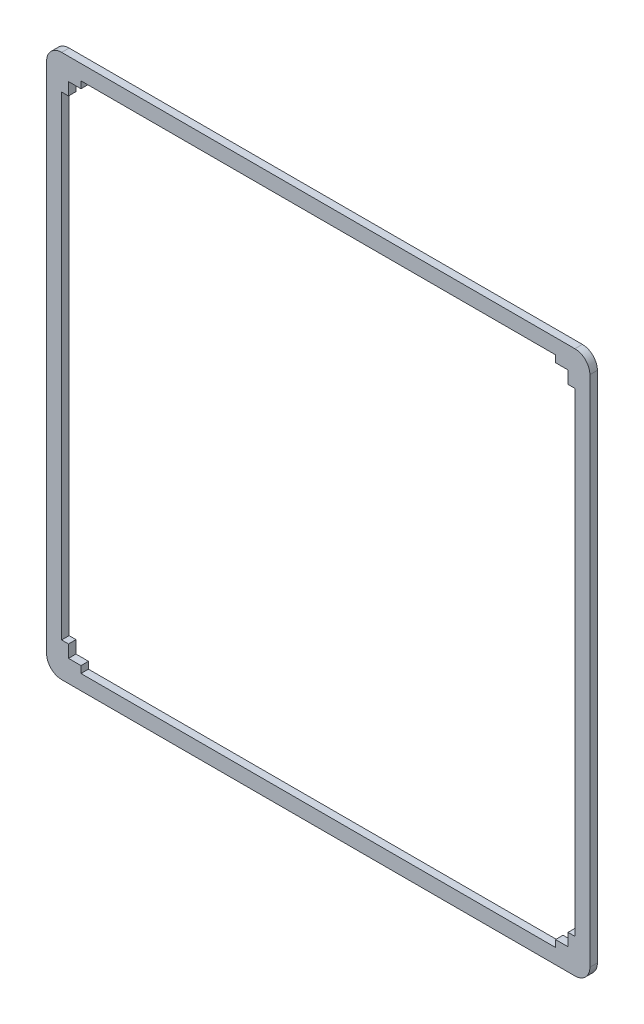
SolidWorks part; units mm, degrees
ref_plane "前视基准面" through (0, 0, 0) normal (0, 0, 1) x (1, 0, 0)
ref_plane "上视基准面" through (0, 0, 0) normal (0, 1, 0) x (1, 0, 0)
ref_plane "右视基准面" through (0, 0, 0) normal (1, 0, 0) x (0, 0, -1)
sketch "草图1" plane through (0, 0, 0) normal (0, 0, 1) x (1, 0, 0)
  line L1 (0, 0) -> (5, 0)
  line L2 (0, 0) -> (0, 5)
  line L3 (0, 200) -> (5, 200)
  line L5 (0, 0) -> (5, 0)
  line L10 (200, 0) -> (200, 5)
  line L14 (0, 0) -> (0, 5)
  line L17 (0, 200) -> (5, 200)
  line L23 (0, 200) -> (5, 200)
  line L25 (0, 0) -> (0, 5)
  line L30 (200, 200) -> (200, 195)
  line L37 (200, 0) -> (200, 5)
  line L44 (200, 0) -> (195, 0)
  line L51 (0, 0) -> (5, 0)
  line L56 (0, 200) -> (0, 195)
  line L60 (208.75, -2.75) -> (208.75, 202.75)
  line L62 (202.75, 208.75) -> (-2.75, 208.75)
  line L64 (-8.75, 202.75) -> (-8.75, -2.75)
  line L66 (-2.75, -8.75) -> (202.75, -8.75)
  line L70 (-2.75, 195) -> (-2.75, 5)
  line L75 (200, 200) -> (200, 195)
  line L80 (0, 200) -> (5, 200)
  line L82 (200, 200) -> (195, 200)
  line L87 (5, 202.75) -> (195, 202.75)
  line L97 (0, 200) -> (0, 195)
  line L102 (200, 200) -> (200, 195)
  line L106 (0, 0) -> (0, 5)
  line L111 (0, 5) -> (0, 0)
  line L113 (202.75, 195) -> (202.75, 5)
  line L116 (200, 0) -> (195, 0)
  line L118 (195, -2.75) -> (5, -2.75)
  line L120 (0, 5) -> (-2.75, 5)
  line L121 (0, 0) -> (5, 0)
  line L122 (5, 0) -> (5, -2.75)
  line L123 (0, 195) -> (0, 200)
  line L124 (195, 0) -> (200, 0)
  line L125 (200, 0) -> (195, 0)
  line L126 (195, 0) -> (195, -2.75)
  line L127 (200, 0) -> (200, 5)
  line L128 (200, 5) -> (202.75, 5)
  line L129 (200, 195) -> (200, 200)
  line L130 (195, 202.75) -> (195, 200)
  line L131 (200, 195) -> (200, 200)
  line L133 (195, 0) -> (200, 0)
  line L134 (202.75, 195) -> (200, 195)
  line L136 (-2.75, 195) -> (0, 195)
  line L137 (195, 200) -> (200, 200)
  line L138 (5, 202.75) -> (5, 200)
  line L139 (195, 200) -> (200, 200)
  line L140 (195, 200) -> (200, 200)
  line L141 (200, 5) -> (200, 0)
  line L142 (200, 5) -> (200, 0)
  line L143 (200, 5) -> (200, 0)
  line L144 (0, 195) -> (0, 200)
  line L146 (200, 5) -> (200, 0)
  line L147 (5, 0) -> (0, 0)
  line L149 (0, 5) -> (0, 0)
  line L174 (200, 200) -> (195, 200)
  line L185 (0, 200) -> (5, 200)
  line L197 (0, 200) -> (0, 195)
  line L210 (0, 200) -> (5, 200)
  line L212 (200, 200) -> (195, 200)
  line L214 (200, 0) -> (195, 0)
  line L216 (0, 0) -> (5, 0)
  line L218 (0, 200) -> (0, 195)
  arc A0 (-8.75, 202.75) -> (-2.75, 208.75) centre (-2.75, 202.75) cw
  arc A2 (208.75, 202.75) -> (202.75, 208.75) centre (202.75, 202.75) ccw
  arc A4 (202.75, -8.75) -> (208.75, -2.75) centre (202.75, -2.75) ccw
  arc A6 (-8.75, -2.75) -> (-2.75, -8.75) centre (-2.75, -2.75) ccw
extrude "凸台-拉伸1" add sketch "草图1" along normal blind 3 contours L64 A6 L66 A4 L60 A2 L62 A0 L138 L87 L130 L82 L30 L134 L113 L128 L10 L44 L126 L118 L122 L1 L2 L120 L70 L136 L56 L3
